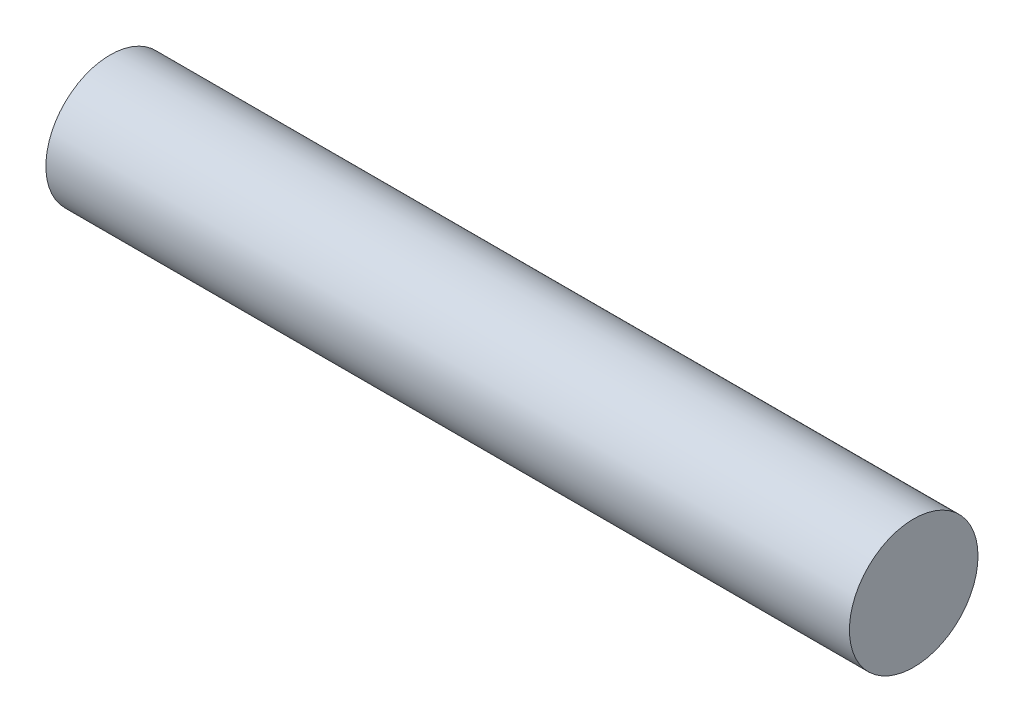
SolidWorks part; units mm, degrees
ref_plane "Front Plane" through (0, 0, 0) normal (0, 0, 1) x (1, 0, 0)
ref_plane "Top Plane" through (0, 0, 0) normal (0, 1, 0) x (1, 0, 0)
ref_plane "Right Plane" through (0, 0, 0) normal (1, 0, 0) x (0, 0, -1)
sketch "Sketch1" plane through (0, 0, 0) normal (1, 0, 0) x (0, 0, -1)
  circle A0 centre (0, 0) radius 8
extrude "Boss-Extrude1" add sketch "Sketch1" along normal blind 100
